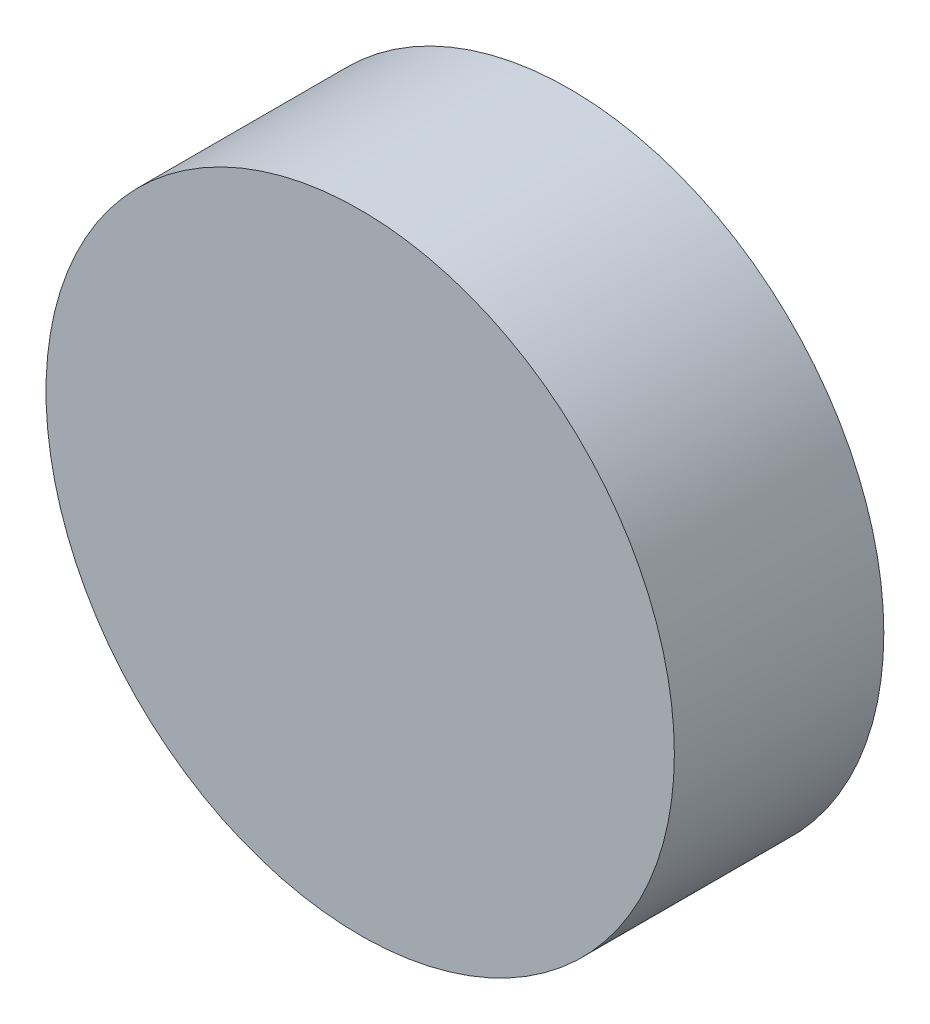
SolidWorks part; units mm, degrees
ref_plane "Front Plane" through (0, 0, 0) normal (0, 0, 1) x (1, 0, 0)
ref_plane "Top Plane" through (0, 0, 0) normal (0, 1, 0) x (1, 0, 0)
ref_plane "Right Plane" through (0, 0, 0) normal (1, 0, 0) x (0, 0, -1)
sketch "Sketch1" plane through (0, 0, 0) normal (0, 0, 1) x (1, 0, 0)
  circle A0 centre (0, 0) radius 60
  dimension "D1" = 120
extrude "Boss-Extrude1" add sketch "Sketch1" along normal blind 40
